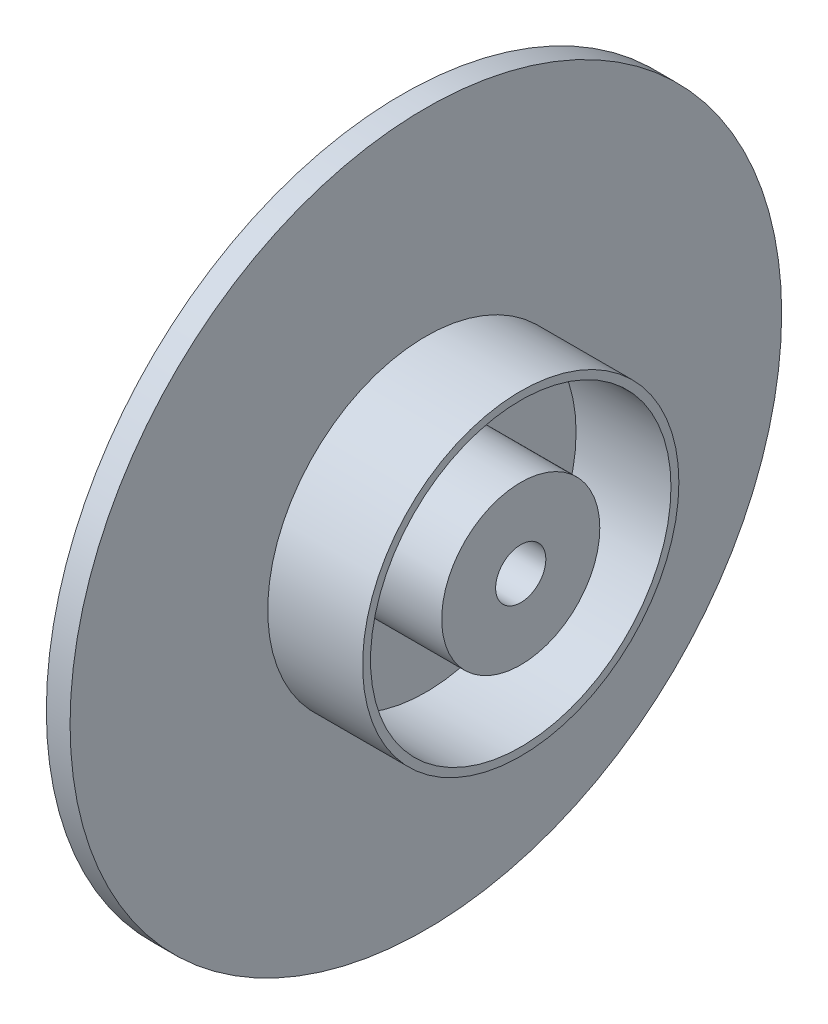
SolidWorks part; units mm, degrees
ref_plane "Front Plane" through (0, 0, 0) normal (0, 0, 1) x (1, 0, 0)
ref_plane "Top Plane" through (0, 0, 0) normal (0, 1, 0) x (1, 0, 0)
ref_plane "Right Plane" through (0, 0, 0) normal (1, 0, 0) x (0, 0, -1)
sketch "Sprocket" plane through (0, 0, 0) normal (1, 0, 0) x (0, 0, -1)
  circle A0 centre (0, 0) radius 45
  dimension "D1" = 90
extrude "Estrusione-Estrusione2" add sketch "Sprocket" along normal blind 3 contours A0
sketch "Schizzo4" plane through (3, 0, 0) normal (1, 0, 0) x (0, 0, -1)
  circle A0 centre (0, 0) radius 10
  dimension "D1" = 20
extrude "Estrusione-Estrusione4" add sketch "Schizzo4" along normal blind 12
sketch "Schizzo5" plane through (3, 0, 0) normal (1, 0, 0) x (0, 0, -1)
  circle A0 centre (0, 0) radius 19
  circle A1 centre (0, 0) radius 20
  circle A2 centre (0, 0) radius 45 construction
  dimension "D1" = 25
  dimension "D2" = 1
extrude "Estrusione-Estrusione5" add sketch "Schizzo5" along normal blind 12
sketch "Schizzo6" plane through (15, 0, 0) normal (1, 0, 0) x (0, 0, -1)
  circle A0 centre (0, 0) radius 3.175
  dimension "D1" = 6.35
extrude "Taglio-Estrusione1" cut sketch "Schizzo6" against normal through all
scale "Scale1" scale about centroid uniform scaling yes scale factor 0.6
equation "\"Thickness6\"=3"
equation "\"D1@Estrusione-Estrusione2\"=\"Thickness6\""
equation "\"D\"=90"
equation "\"D1@Sprocket\"=\"D\""
equation "\"Side_w\"=12"
equation "\"D1@Estrusione-Estrusione4\"=\"Side_w\""
equation "\"D1@Estrusione-Estrusione5\"=\"Side_w\""
